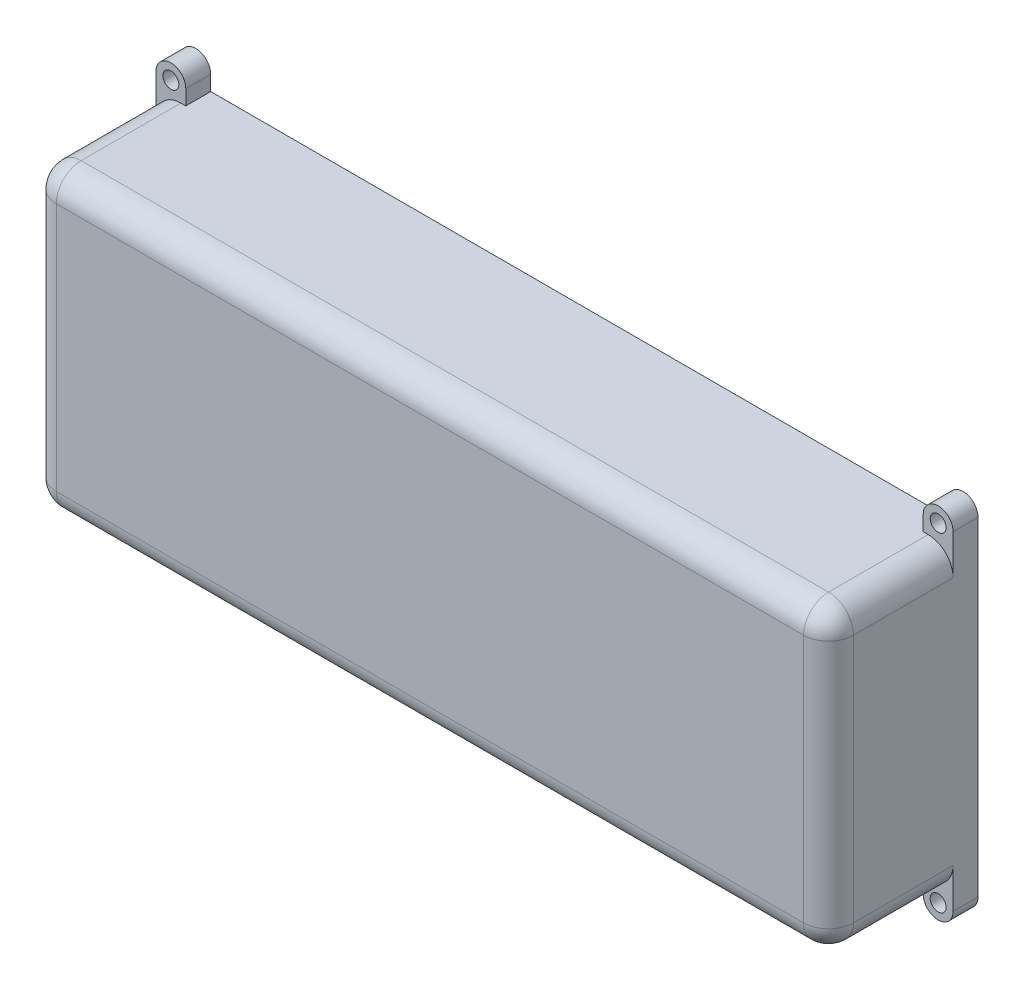
SolidWorks part; units mm, degrees
ref_plane "Front Plane" through (0, 0, 0) normal (0, 0, 1) x (1, 0, 0)
ref_plane "Top Plane" through (0, 0, 0) normal (0, 1, 0) x (1, 0, 0)
ref_plane "Right Plane" through (0, 0, 0) normal (1, 0, 0) x (0, 0, -1)
sketch "Sketch1" plane through (0, 0, 0) normal (0, 0, 1) x (1, 0, 0)
  line L0 (-80, 50) -> (-80, -50) construction
  line L1 (-80, -30) -> (-75, -30)
  line L2 (-80, -30) -> (-80, 30)
  line L3 (-80, 30) -> (-75, 30)
  line L4 (-75, -30) -> (-75, 30)
  line L6 (-75, -30) -> (80, -30)
  line L7 (-75, -30) -> (-75, -25)
  line L8 (-75, -25) -> (80, -25)
  line L9 (80, -30) -> (80, -25)
  line L10 (80, 50) -> (80, -50) construction
  line L11 (16.5, 0) -> (-16.5, 0) construction
  line L12 (-75, 30) -> (80, 30)
  line L13 (-75, 30) -> (-75, 25)
  line L14 (-75, 25) -> (80, 25)
  line L15 (80, 30) -> (80, 25)
  line L16 (80, -25) -> (75, -25)
  line L17 (80, -25) -> (80, 25)
  line L18 (80, 25) -> (75, 25)
  line L19 (75, -25) -> (75, 25)
  line L20 (63, -25) -> (65, -25)
  line L21 (63, -25) -> (63, -15)
  line L22 (63, -15) -> (65, -15)
  line L23 (65, -25) -> (65, -15)
  line L24 (63, 15) -> (65, 15)
  line L25 (65, 25) -> (65, 15)
  line L26 (63, 25) -> (65, 25)
  line L27 (63, 25) -> (63, 15)
  point P6 (-80, 0)
  point P7 (-80, 0)
  dimension "D1" = 60
  dimension "D2" = 5
  dimension "D3" = 5
  dimension "D4" = 155
  dimension "D5" = 5
  dimension "D6" = 155
  dimension "D7" = 5
  dimension "D8" = 10
  dimension "D9" = 2
  dimension "D10" = 138
extrude "Boss-Extrude1" add sketch "Sketch1" along normal blind 25 contours L19 L8 L17 L14 | L6 L9 L8 L4 | L1 L4 L3 L2 | L15 L12 L4 L14 | L23 L22 L21 L20 | L27 L24 L25 L26
sketch "Sketch2" plane through (0, 0, 25) normal (0, 0, 1) x (1, 0, 0)
  line L4 (-80, 30) -> (-80, -30)
  line L5 (-80, -30) -> (80, -30)
  line L6 (80, -30) -> (80, 30)
  line L7 (80, 30) -> (-80, 30)
  line L8 (-80, 30) -> (-80, -30)
  line L9 (-80, -30) -> (80, -30)
  line L10 (80, -30) -> (80, 30)
  line L11 (80, 30) -> (-80, 30)
  dimension "D1" = 0
extrude "Boss-Extrude2" add sketch "Sketch2" along normal blind 5
sketch "Sketch5" plane through (0, 0, 0) normal (0, 0, -1) x (-1, 0, 0)
  line L0 (80, -33) -> (80, -30)
  line L1 (74, -33) -> (74, -30)
  line L2 (80, -30) -> (-80, -30) construction
  line L3 (74, -30) -> (80, -30)
  circle A0 centre (77, -33) radius 1.6
  circle A1 centre (77, -33) radius 3
  line M20 (-80, -30) -> (80, -30)
  dimension "D1" = 3.2
  dimension "D2" = 6
extrude "Boss-Extrude3" add sketch "Sketch5" against normal blind 5 contours A1 A0 | A1 L0 L3 | A1 L1 M20
mirror "Mirror1" about plane through (0, 0, 0) normal (1, 0, 0) of "Boss-Extrude3"
mirror "Mirror2" about plane through (0, 0, 0) normal (0, 1, 0) of "Mirror1", "Boss-Extrude3"
fillet "Fillet1" radius 5 8 edges at (80, 0, 30) (0, -30, 30) (-80, 0, 30) (0, 30, 30) (-80, -30, 17.5) (-80, 30, 17.5) (80, -30, 17.5) (80, 30, 17.5)
